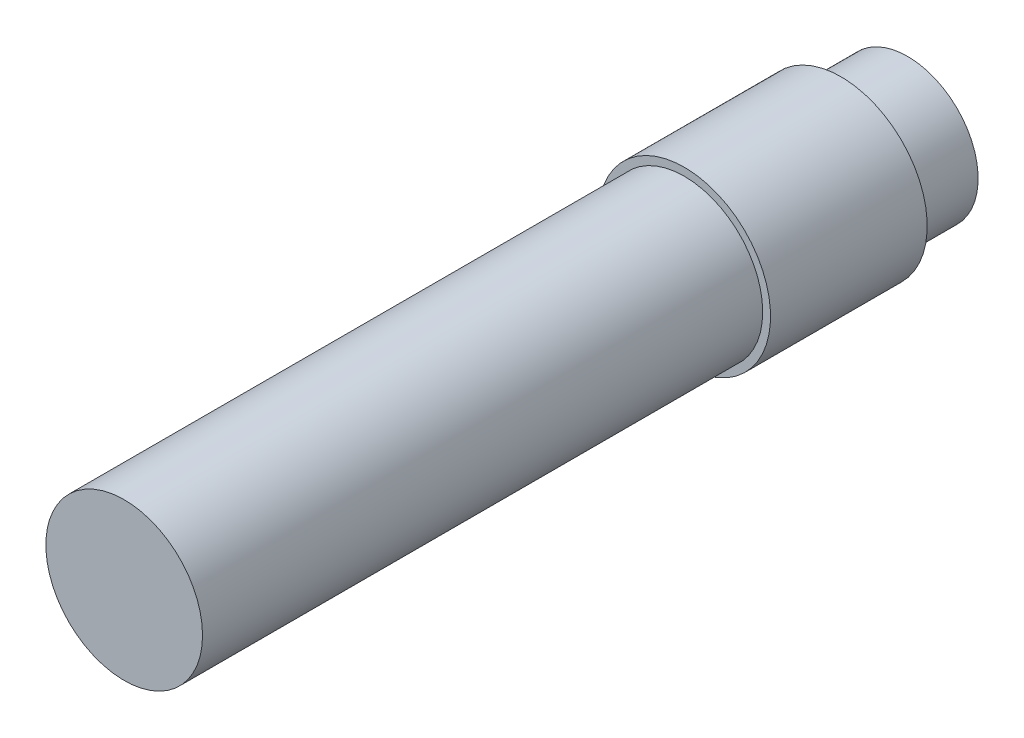
SolidWorks part; units mm, degrees
material "純碳鋼"
ref_plane "前基準面" through (0, 0, 0) normal (0, 0, 1) x (1, 0, 0)
ref_plane "上基準面" through (0, 0, 0) normal (0, 1, 0) x (1, 0, 0)
ref_plane "右基準面" through (0, 0, 0) normal (1, 0, 0) x (0, 0, -1)
sketch "草圖1" plane through (0, 0, 0) normal (0, 0, 1) x (1, 0, 0)
  circle A0 centre (0, 0) radius 11
  dimension "D1" = 22
extrude "填料-伸長1" add sketch "草圖1" along normal blind 100
sketch "草圖2" plane through (0, 0, 0) normal (0, 0, -1) x (-1, 0, 0)
  circle A0 centre (0, 0) radius 11
  circle A1 centre (0, 0) radius 9
  circle A2 centre (0, 0) radius 11 construction
  dimension "D1" = 18
extrude "除料-伸長1" cut sketch "草圖2" against normal blind 8.5
sketch "草圖3" plane through (0, 0, 100) normal (0, 0, 1) x (1, 0, 0)
  circle A0 centre (0, 0) radius 11
  circle A1 centre (0, 0) radius 10
  circle A2 centre (0, 0) radius 11 construction
  dimension "D1" = 20
extrude "除料-伸長2" cut sketch "草圖3" against normal offset from surface (71.5 mm away) 20 up to face at (-9, 0, 8.5)
